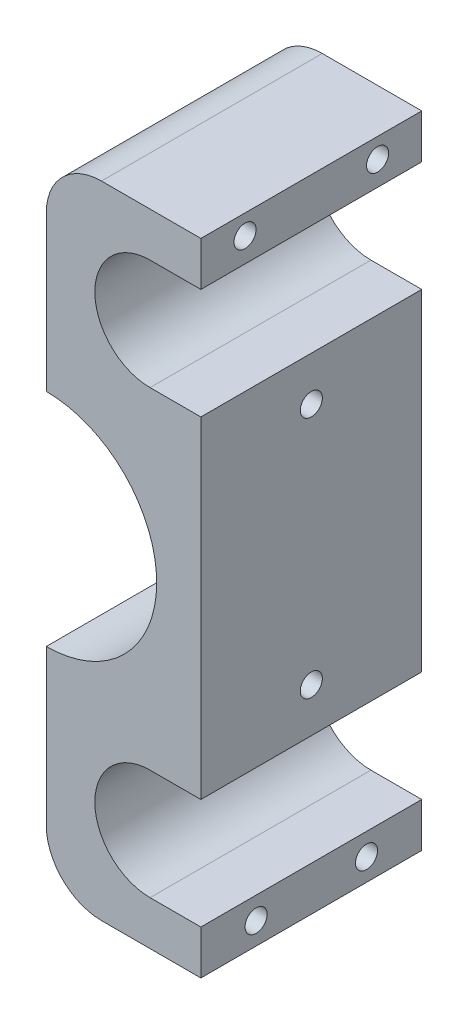
SolidWorks part; units mm, degrees
ref_plane "前视基准面" through (0, 0, 0) normal (0, 0, 1) x (1, 0, 0)
ref_plane "上视基准面" through (0, 0, 0) normal (0, 1, 0) x (1, 0, 0)
ref_plane "右视基准面" through (0, 0, 0) normal (1, 0, 0) x (0, 0, -1)
sketch "草图1" plane through (0, 0, 0) normal (0, 0, 1) x (1, 0, 0)
  line L0 (0, 29) -> (0, 25)
  line L1 (-14, 29) -> (-14, -29)
  line L2 (0, -29) -> (-14, -29)
  line L4 (0, 29) -> (-14, 29)
  line L5 (0, -25) -> (0, -29)
  line L6 (-4.6, 25) -> (0, 25)
  line L7 (-4.6, 15) -> (0, 15)
  line L8 (-4.6, -15) -> (0, -15)
  line L9 (-4.6, -25) -> (0, -25)
  line L11 (0, 15) -> (0, -15)
  arc A0 (-4.6, 25) -> (-4.6, 15) centre (-4.6, 20) ccw
  arc A1 (-4.6, -15) -> (-4.6, -25) centre (-4.6, -20) ccw
  point P5 (-9.1044, -17.8298)
  point P7 (0, 28)
  point P8 (-30.8029, 28)
  dimension "D6" = 10
  dimension "D7" = 10
  dimension "D4" = 4.6
  dimension "D3" = 40
  dimension "D1" = 58
  dimension "D2" = 20
extrude "凸台-拉伸1" add sketch "草图1" along normal blind 20
fillet "圆角1" radius 5 2 edges at (-14, -29, 10) (-14, 29, 10)
sketch "草图2" plane through (0, 0, 0) normal (1, 0, 0) x (0, 0, -1)
  line L0 (-20, 15) -> (0, 15) construction
  line L1 (-20, -15) -> (0, -15) construction
  line L2 (-20, -29) -> (0, -29) construction
  line L3 (0, -29) -> (0, -25) construction
  line L4 (-20, -29) -> (-20, -25) construction
  line L5 (-20, 25) -> (-20, 29) construction
  line L6 (0, 25) -> (0, 29) construction
  line L7 (-20, 25) -> (0, 25) construction
  line L8 (-20, 25) -> (0, 25) construction
  line L9 (0, -15) -> (0, 15) construction
  circle A0 centre (-16, 27.2) radius 1
  circle A1 centre (-4, 27.2) radius 1
  circle A2 centre (-10, 11) radius 1
  circle A3 centre (-10, -11) radius 1
  circle A4 centre (-15, -27) radius 1
  circle A5 centre (-5, -27) radius 1
  dimension "D1" = 2
  dimension "D2" = 2
  dimension "D3" = 2
  dimension "D4" = 2
  dimension "D5" = 2
  dimension "D6" = 2
  dimension "D7" = 4
  dimension "D8" = 4
  dimension "D9" = 2
  dimension "D10" = 2
  dimension "D11" = 5
  dimension "D12" = 5
  dimension "D13" = 4
  dimension "D14" = 4
  dimension "D15" = 2.2
  dimension "D16" = 2.2
  dimension "D17" = 10
  dimension "D18" = 10
extrude "切除-拉伸1" cut sketch "草图2" against normal blind 10
sketch "草图3" plane through (0, 0, 20) normal (0, 0, 1) x (1, 0, 0)
  line L0 (-14, 24) -> (-14, -24) construction
  circle A0 centre (-14, 0) radius 10
  dimension "D1" = 20
extrude "切除-拉伸2" cut sketch "草图3" against normal blind 40
